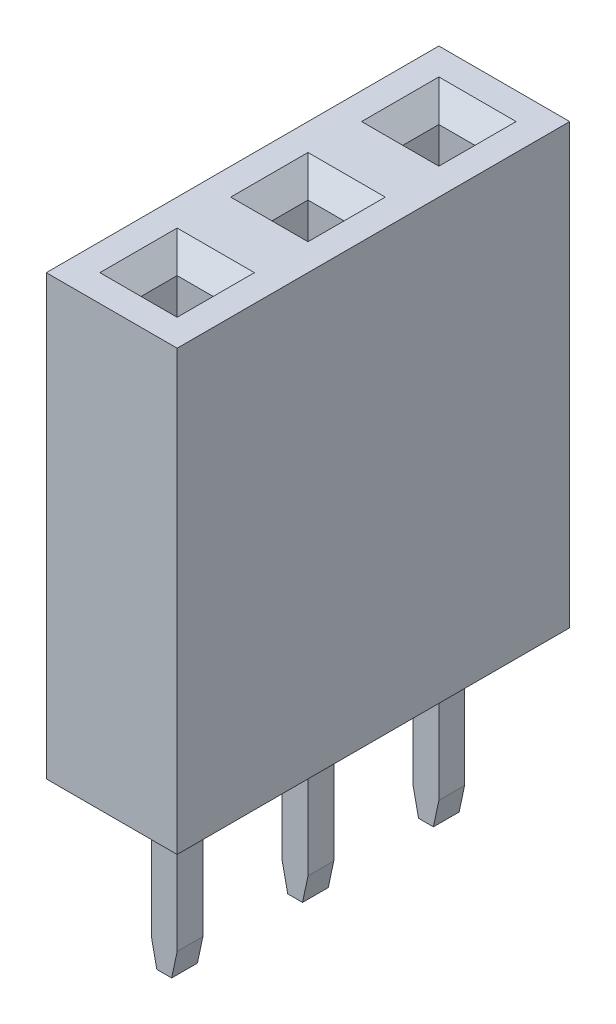
SolidWorks part; units mm, degrees
ref_plane "Спереди" through (0, 0, 0) normal (0, 0, 1) x (1, 0, 0)
ref_plane "Сверху" through (0, 0, 0) normal (0, 1, 0) x (1, 0, 0)
ref_plane "Справа" through (0, 0, 0) normal (1, 0, 0) x (0, 0, -1)
ref_plane "Плоскость1" through (0, 0, 0) normal (0, 1, 0) x (-1, 0, 0)
sketch "Эскиз1" plane through (0, 0, 0) normal (0, 1, 0) x (-1, 0, 0)
  line L0 (0, 0) -> (-5.5295, 0) construction
  line L1 (0, 0) -> (0, -2.1715) construction
  line L2 (-1.27, 1.27) -> (1.27, 1.27)
  line L3 (-1.27, 1.27) -> (-1.27, -1.27)
  line L4 (-1.27, -1.27) -> (1.27, -1.27)
  line L5 (1.27, 1.27) -> (1.27, -1.27)
  point P0 (-1.27, 1.27)
  point P1 (1.27, -1.27)
  point P2 (-1.27, -1.27)
  point P3 (1.27, 1.27)
  dimension "D1" = 2.54
  dimension "D6" = 1.27
extrude "Бобышка-Вытянуть1" add sketch "Эскиз1" along normal blind 8.51
sketch "Эскиз4" plane through (0, 8.51, 0) normal (0, 1, 0) x (1, 0, 0)
  line L0 (0, 0) -> (0.806, 0) construction
  line L1 (0, 0) -> (0, 1.2961) construction
  line L3 (-0.35, 0.35) -> (0.35, 0.35)
  line L4 (-0.35, 0.35) -> (-0.35, -0.35)
  line L5 (-0.35, -0.35) -> (0.35, -0.35)
  line L6 (0.35, 0.35) -> (0.35, -0.35)
  dimension "D1" = 0.7
extrude "Вырез-Вытянуть1" cut sketch "Эскиз4" against normal blind 8.21
chamfer "Фаска3" distance 0.4 angle 45 4 edges at (0.35, 8.51, 0) (0, 8.51, -0.35) (0, 8.51, 0.35) (-0.35, 8.51, 0)
sketch "Эскиз2" plane through (0, 0, 0) normal (0, 1, 0) x (-1, 0, 0)
  line L0 (0, 0) -> (0, -0.4454) construction
  line L1 (0.25, 0.25) -> (-0.25, 0.25)
  line L2 (0.25, 0.25) -> (0.25, -0.25)
  line L3 (0.25, -0.25) -> (-0.25, -0.25)
  line L4 (-0.25, 0.25) -> (-0.25, -0.25)
  line L5 (0, 0) -> (-0.4704, 0) construction
  dimension "D1" = 0.5
  dimension "D2" = 0.5
extrude "Бобышка-Вытянуть2" add sketch "Эскиз2" against normal blind 3.15
chamfer "Фаска2" distance 0.5 angle 12 2 edges at (0.25, -3.15, 0) (-0.25, -3.15, 0)
pattern_linear "Линейный массив1" count 3 spacing 2.54 along (0, 0, -1) of "Бобышка-Вытянуть1", "Вырез-Вытянуть1", "Фаска3", "Бобышка-Вытянуть2", "Фаска2"
equation "\"D6@Эскиз1\"=2.54/2"
